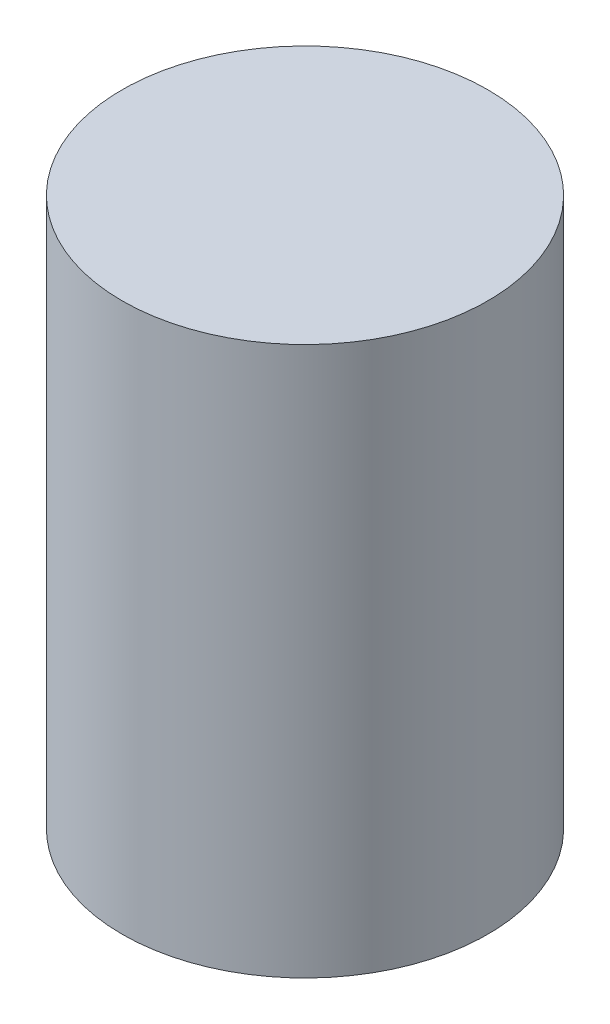
SolidWorks part; units mm, degrees
ref_plane "Front Plane" through (0, 0, 0) normal (0, 0, 1) x (1, 0, 0)
ref_plane "Top Plane" through (0, 0, 0) normal (0, 1, 0) x (1, 0, 0)
ref_plane "Right Plane" through (0, 0, 0) normal (1, 0, 0) x (0, 0, -1)
sketch "Sketch1" plane through (0, 0, 0) normal (0, 1, 0) x (1, 0, 0)
  circle A0 centre (0, 0) radius 1.524
extrude "Boss-Extrude1" add sketch "Sketch1" along normal blind 4.572
